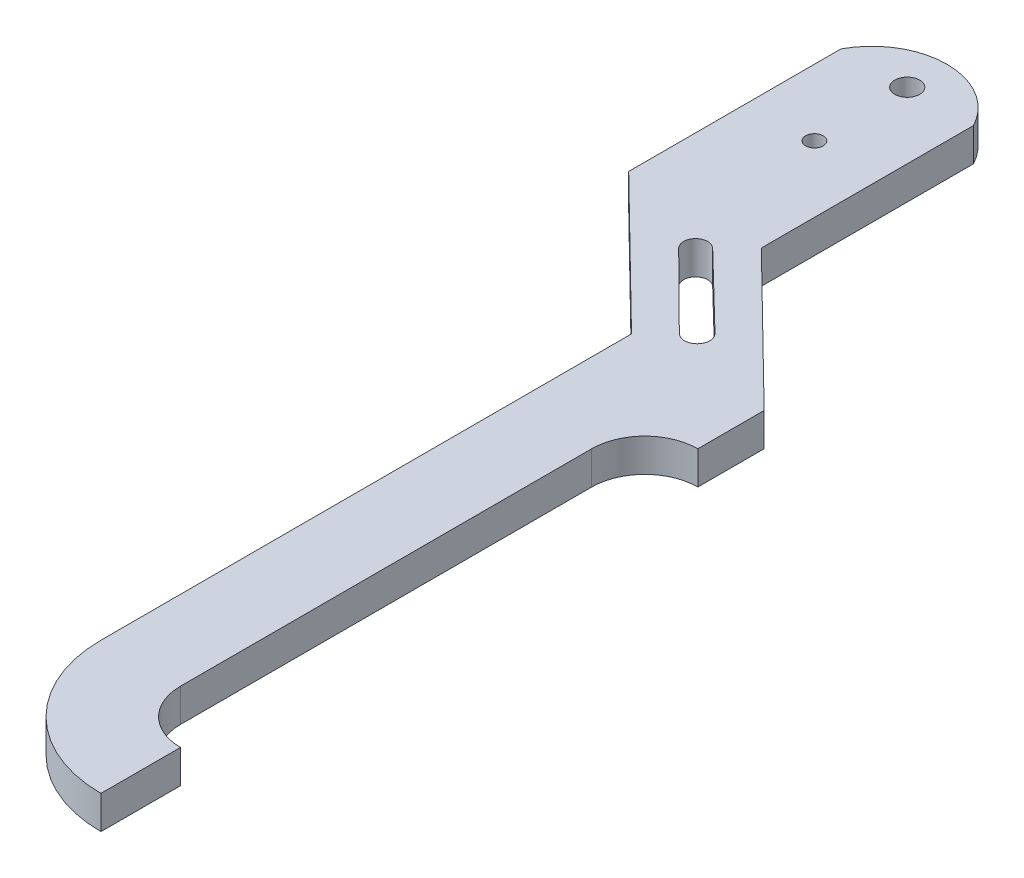
SolidWorks part; units mm, degrees
ref_plane "Front Plane" through (0, 0, 0) normal (0, 0, 1) x (1, 0, 0)
ref_plane "Top Plane" through (0, 0, 0) normal (0, 1, 0) x (1, 0, 0)
ref_plane "Right Plane" through (0, 0, 0) normal (1, 0, 0) x (0, 0, -1)
sketch "Sketch1" plane through (0, 0, 0) normal (0, 1, 0) x (1, 0, 0)
  line L0 (-13.027, 16.3908) -> (-13.027, 36.7108)
  line L1 (-2.6329, 14.0383) -> (4.5296, 7.0977)
  line L2 (2.8433, 5.3674) -> (-4.2441, 12.3946)
  line L3 (8.1974, -8.3742) -> (8.1974, -47.7442)
  line L4 (0.5774, 3.0558) -> (0.5774, -47.7442)
  line L6 (-13.027, 16.3908) -> (0.5774, 3.0558)
  line L7 (13.2774, 3.0558) -> (13.2774, -3.2942)
  line L8 (-0.327, 36.7108) -> (-0.327, 16.3908)
  line L9 (-0.327, 16.3908) -> (13.2774, 3.0558)
  line L11 (13.2774, -52.8242) -> (13.2774, -60.4442)
  circle A0 centre (-6.677, 27.8208) radius 0.8401
  arc A1 (2.8433, 5.3674) -> (4.5296, 7.0977) centre (3.6864, 6.2326) ccw
  arc A2 (13.2774, -3.2942) -> (8.1974, -8.3742) centre (13.2774, -8.3742) ccw
  arc A3 (0.5774, -47.7442) -> (13.2774, -60.4442) centre (13.2774, -47.7442) ccw
  arc A4 (8.1974, -47.7442) -> (13.2774, -52.8242) centre (13.2774, -47.7442) ccw
  circle A5 centre (-6.677, 36.7108) radius 1.1906
  arc A6 (-4.2441, 12.3946) -> (-2.6329, 14.0383) centre (-3.4385, 13.2164) cw
  arc A7 (-6.677, 40.5208) -> (-13.027, 36.7108) centre (-6.677, 33.3241) ccw
  arc A8 (-6.677, 40.5208) -> (-0.327, 36.7108) centre (-6.677, 33.3241) cw
  dimension "D1" = 1.6802
  dimension "D2" = 2.3813
  dimension "D9" = 5.08
  dimension "D4" = 12.7
  dimension "D7" = 5.08
  dimension "D3" = 50.8
  dimension "D5" = 19.05
  dimension "D6" = 6.35
  dimension "D8" = 39.37
  dimension "D12" = 19.05
extrude "Boss-Extrude1" add sketch "Sketch1" along normal blind 3.175
